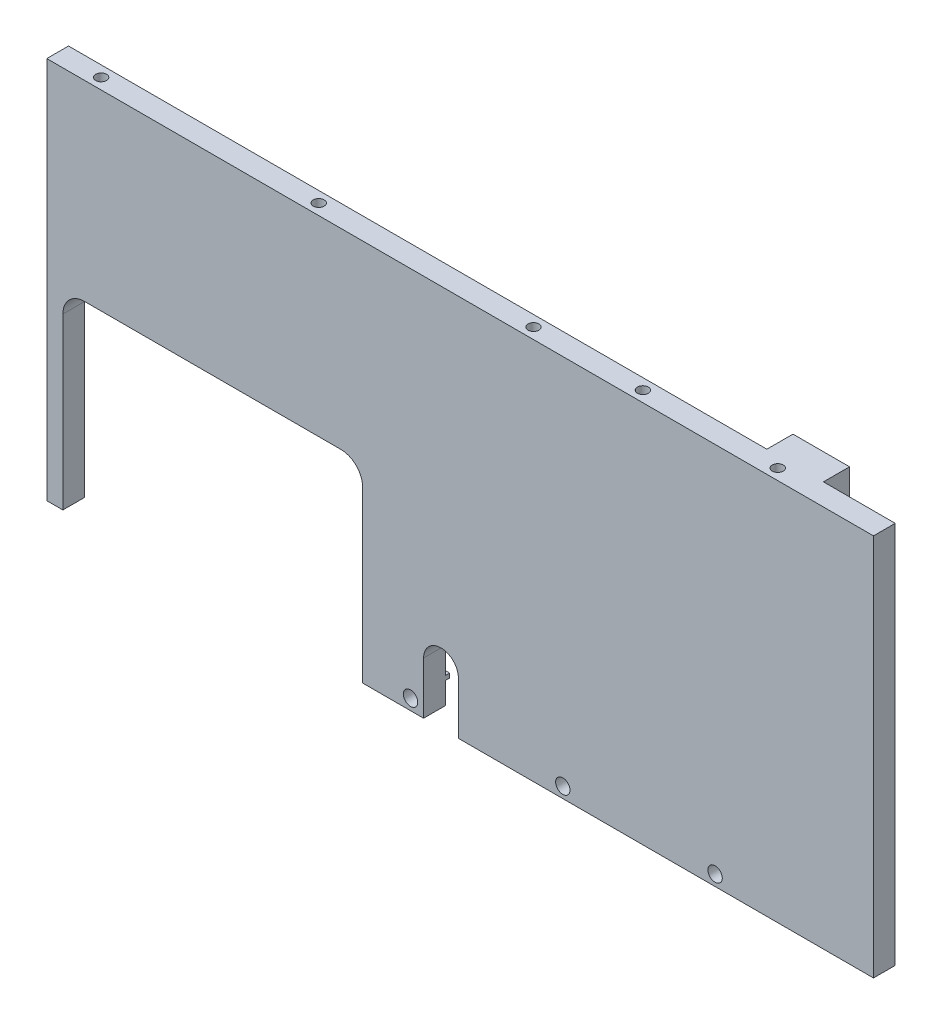
SolidWorks part; units mm, degrees
ref_plane "Front Plane" through (0, 0, 0) normal (0, 0, 1) x (1, 0, 0)
ref_plane "Top Plane" through (0, 0, 0) normal (0, 1, 0) x (1, 0, 0)
ref_plane "Right Plane" through (0, 0, 0) normal (1, 0, 0) x (0, 0, -1)
sketch "Sketch1" plane through (0, 0, 0) normal (0, 0, 1) x (1, 0, 0)
  line L1 (-95, 44) -> (95, 44)
  line L2 (-95, 44) -> (-95, -44)
  line L3 (-95, -44) -> (95, -44)
  line L4 (95, 44) -> (95, -44)
  line L5 (-95, 44) -> (95, -44) construction
  line L6 (-95, -44) -> (95, 44) construction
  point P0 (0, 0)
  dimension "D1" = 190
  dimension "D2" = 88
extrude "Boss-Extrude1" add sketch "Sketch1" along normal blind 5
sketch "Sketch2" plane through (0, 0, 0) normal (0, 0, -1) x (-1, 0, 0)
  line L0 (-95, 44) -> (95, 44) construction
  line L1 (-78.5, 44) -> (-65.5, 44)
  line L2 (-78.5, 44) -> (-78.5, -39)
  line L3 (-78.5, -39) -> (-65.5, -39)
  line L4 (-65.5, 44) -> (-65.5, -39)
  line L5 (95, -44) -> (-95, -44) construction
  line L6 (-95, -44) -> (-95, 44) construction
  dimension "D1" = 13
  dimension "D2" = 16.5
  dimension "D3" = 5
extrude "Boss-Extrude2" add sketch "Sketch2" along normal blind 6
sketch "Sketch4" plane through (0, 0, 0) normal (0, 0, -1) x (-1, 0, 0)
  line L8 (-65.5, -38) -> (14, -38)
  line L9 (-65.5, -39) -> (-65.5, 44) construction
  line L10 (14, -38) -> (14, -34)
  line L11 (14, -34) -> (15, -34)
  line L12 (15, -34) -> (15, -39)
  line L13 (15, -39) -> (-65.5, -39)
  line L14 (-65.5, -39) -> (-65.5, -38)
  dimension "D1" = 1
  dimension "D2" = 80.5
  dimension "D3" = 5
extrude "Boss-Extrude3" add sketch "Sketch4" along normal blind 1
sketch "Sketch7" plane through (0, 0, 0) normal (0, 0, -1) x (-1, 0, 0)
  line L0 (11.4, -41.5) -> (-23.6, -41.5) construction
  line L1 (-23.6, -41.5) -> (-58.6, -41.5) construction
  line L2 (15, -39) -> (15, -34) construction
  line L3 (95, -44) -> (-95, -44) construction
  circle A0 centre (-58.6, -41.5) radius 1.65
  circle A1 centre (-23.6, -41.5) radius 1.65
  circle A2 centre (11.4, -41.5) radius 1.65
  dimension "D1" = 3.3
  dimension "D3" = 2.5
  dimension "D2" = 3.6
  dimension "D4" = 35
extrude "Cut-Extrude3" cut sketch "Sketch7" against normal through all
fillet "Fillet3" radius 2 1 edges at (-14, -38, -0.5)
sketch "草图1" plane through (0, 44, 0) normal (0, 1, 0) x (1, 0, 0)
  line L0 (-95, -2.5) -> (-85, -2.5) construction
  line L1 (-95, -5) -> (-95, 0) construction
  line L2 (-85, -2.5) -> (-35, -2.5) construction
  line L3 (-35, -2.5) -> (15, -2.5) construction
  line L4 (15, -2.5) -> (39.5, -2.5) construction
  line L5 (39.5, -2.5) -> (70.5, -2.5) construction
  line L6 (78.5, 6) -> (78.5, 0) construction
  dimension "D1" = 8
  dimension "D2" = 31
  dimension "D3" = 10
  dimension "D4" = 50
hole_wizard "M3 螺纹孔1" positions "3D草图1" profile "草图2" tap size "M3" standard "ISO"
sketch3d "3D草图1"
  line L0 (-35, 44, 2.5) -> (15, 44, 2.5) construction
  point P0 (-85, 44, 2.5)
  point P3 (-35, 44, 2.5)
  point P6 (14.3733, 44, 2.5)
  point P10 (39.5, 44, 2.5)
  point P13 (70.5, 44, 2.5)
sketch "草图2" plane through (-85, 44, 2.5) normal (1, 0, 0) x (0, 0, 1)
  line L0 (0, 0) -> (0, 9.2511)
  line L1 (0, 9.2511) -> (1.25, 8.5)
  line L2 (1.25, 8.5) -> (1.25, 0)
  line L5 (1.25, 0) -> (0, 0)
  line L10 (0, 9.2511) -> (-1.25, 8.5) construction
  line L11 (0, -6.35) -> (0, 107.95) construction
  dimension "螺纹孔钻头直径" = 2.5
  dimension "螺纹孔钻头深度" = 8.5
  dimension "导头角度" = 118
cosmetic thread "孔螺蚊线1" parameters "D1"=6, "D2"=3
cosmetic thread "孔螺蚊线2" parameters "D1"=6, "D2"=3
cosmetic thread "孔螺蚊线3" parameters "D1"=6, "D2"=3
cosmetic thread "孔螺蚊线4" parameters "D1"=6, "D2"=3
cosmetic thread "孔螺蚊线5" parameters "D1"=6, "D2"=3
sketch "草图3" plane through (0, 0, 0) normal (0, 0, -1) x (-1, 0, 0)
  line L0 (0.4, -44) -> (0.4, -32)
  line L1 (95, -44) -> (-95, -44) construction
  line L2 (8.4, -32) -> (8.4, -44)
  line L3 (8.4, -44) -> (0.4, -44)
  line L4 (12, -38) -> (-65.5, -38) construction
  arc A0 (0.4, -32) -> (8.4, -32) centre (4.4, -32) cw
  circle A1 centre (11.4, -41.5) radius 1.65 construction
  dimension "D1" = 3
  dimension "D2" = 8
  dimension "D3" = 6
extrude "切除-拉伸1" cut sketch "草图3" along normal through all from surface at -5 starting at face at (56.95, -41.5, 5)
sketch "草图4" plane through (0, 0, 5) normal (0, 0, 1) x (1, 0, 0)
  line L0 (-95, -44) -> (-8.4, -44) construction
  line L1 (-91.3, 0) -> (-22.4, 0)
  line L2 (-91.3, 0) -> (-91.3, -44)
  line L3 (-91.3, -44) -> (-22.4, -44)
  line L4 (-22.4, 0) -> (-22.4, -44)
  line L5 (-95, 44) -> (-95, -44) construction
  dimension "D1" = 44
  dimension "D2" = 68.9
  dimension "D3" = 3.7
extrude "切除-拉伸2" cut sketch "草图4" against normal through all
fillet "圆角1" radius 5 2 edges at (-91.3, 0, 2.5) (-22.4, 0, 2.5)
